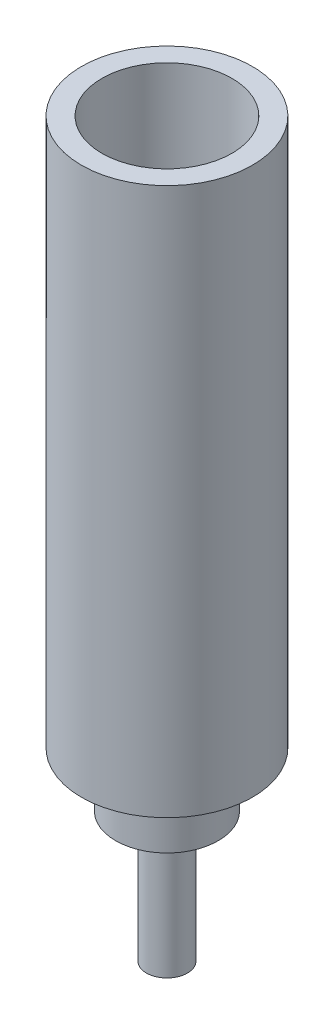
SolidWorks part; units mm, degrees
ref_plane "Plano frontal" through (0, 0, 0) normal (0, 0, 1) x (1, 0, 0)
ref_plane "Plano superior" through (0, 0, 0) normal (0, 1, 0) x (1, 0, 0)
ref_plane "Plano direito" through (0, 0, 0) normal (1, 0, 0) x (0, 0, -1)
sketch "Esboço2" plane through (0, 0, 0) normal (0, 0, 1) x (1, 0, 0)
  line L0 (0, 98.35) -> (0, 0) construction
  line L1 (-12.5, 107) -> (-12.5, 27)
  line L2 (-12.5, 27) -> (-7.5, 27)
  line L3 (-3, 19) -> (-3, 0)
  line L4 (-9.5, 107) -> (-9.5, 32)
  line L5 (-9.5, 32) -> (0, 32)
  line L6 (-9.5, 107) -> (-12.5, 107)
  line L7 (-3, 0) -> (0, 0)
  line L8 (-7.5, 27) -> (-7.5, 19)
  line L9 (-7.5, 19) -> (-3, 19)
  line L10 (0, 0) -> (0, 32)
  dimension "D1" = 25
  dimension "D2" = 3
  dimension "D3" = 5
  dimension "D4" = 8
  dimension "D5" = 6
  dimension "D6" = 80
  dimension "D7" = 15
  dimension "D8" = 19
revolve "Revolução1" add sketch "Esboço2" angle 360 about L0
